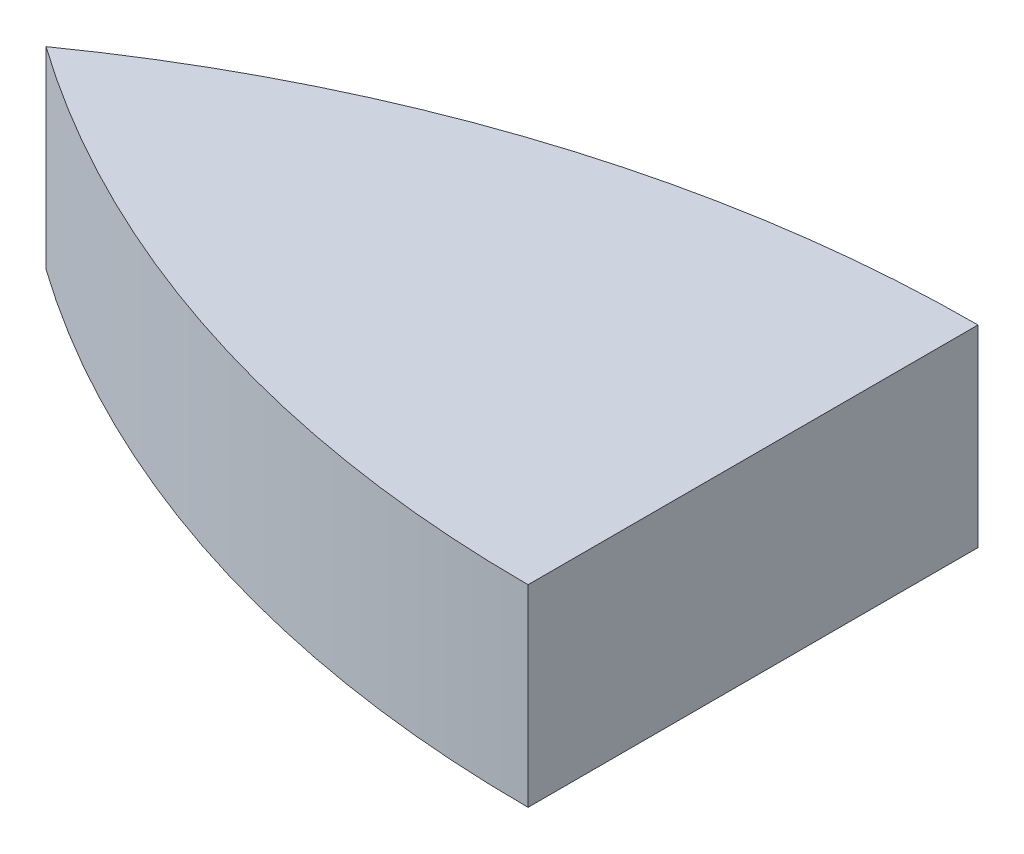
SolidWorks part; units mm, degrees
ref_plane "Front Plane" through (0, 0, 0) normal (0, 0, 1) x (1, 0, 0)
ref_plane "Top Plane" through (0, 0, 0) normal (0, 1, 0) x (1, 0, 0)
ref_plane "Right Plane" through (0, 0, 0) normal (1, 0, 0) x (0, 0, -1)
sketch "Sketch2" plane through (0, 0, 0) normal (0, 1, 0) x (1, 0, 0)
  line L0 (13.2615, 1.75) -> (13.2615, -1.75)
  line L1 (-55, 0) -> (55, 0) construction
  arc A0 (13.2615, -1.75) -> (7.7615, 0) centre (13.2615, 7.7679) cw
  arc A1 (13.2615, 1.75) -> (7.7615, 0) centre (13.2615, -7.7679) ccw
  dimension "D1" = 3.5
  dimension "D2" = 1.75
  dimension "D3" = 5.5
extrude "Boss-Extrude1" add sketch "Sketch2" along normal blind 1.5
